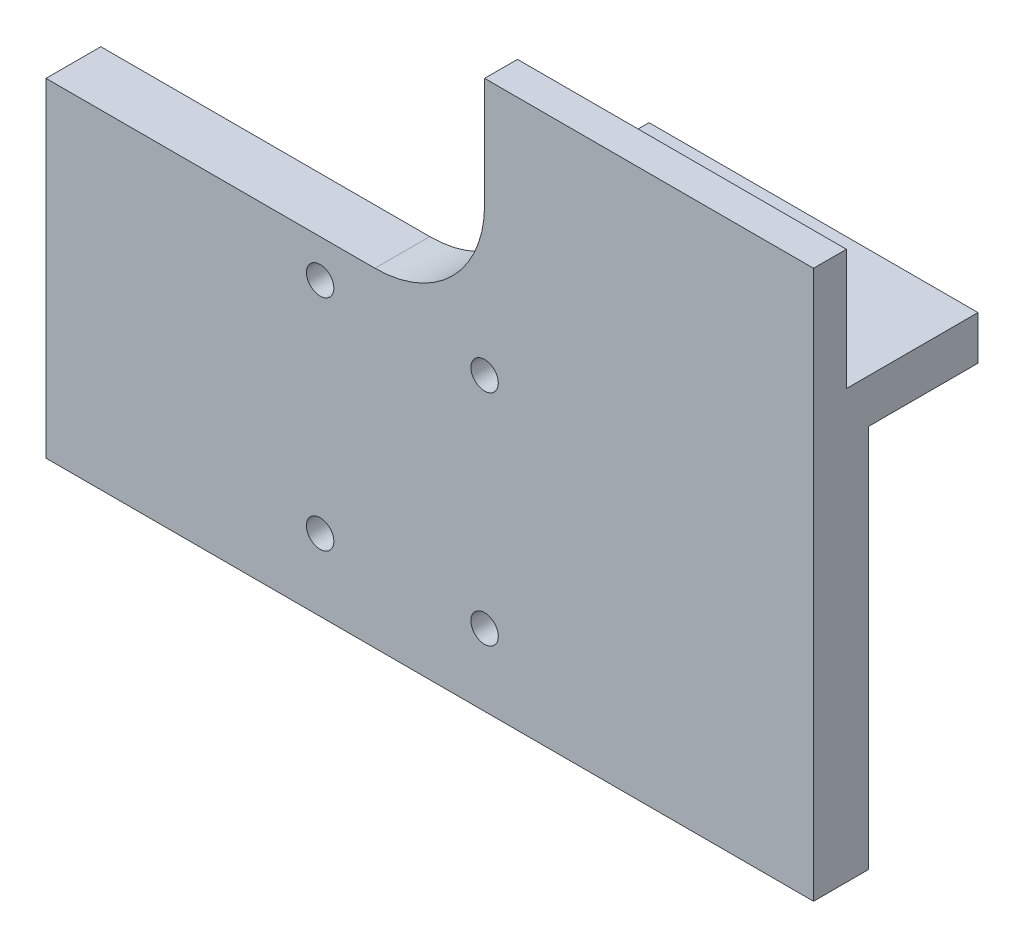
SolidWorks part; units mm, degrees
ref_plane "Front Plane" through (0, 0, 0) normal (0, 0, 1) x (1, 0, 0)
ref_plane "Top Plane" through (0, 0, 0) normal (0, 1, 0) x (1, 0, 0)
ref_plane "Right Plane" through (0, 0, 0) normal (1, 0, 0) x (0, 0, -1)
sketch "Sketch1" plane through (0, 0, 0) normal (0, 0, 1) x (1, 0, 0)
  line L0 (0, 0) -> (70, 0)
  line L1 (0, 0) -> (0, 30)
  line L2 (0, 30) -> (30, 30)
  line L4 (70, 50) -> (70, 0)
  line L5 (40, 40) -> (40, 50)
  line L6 (40, 50) -> (70, 50)
  arc A0 (30, 30) -> (40, 40) centre (30, 40) ccw
  dimension "D2" = 10
  dimension "D3" = 50
  dimension "D1" = 70
  dimension "D5" = 30
  dimension "D6" = 30
extrude "Body" add sketch "Sketch1" along normal blind 5
hole_wizard "M3x0.5 Tapped Hole1" positions "Sketch7" profile "Sketch8" tap size "M3x0.5" standard "ANSI Metric" end condition through all
sketch "Sketch7" plane through (0, 0, 5) normal (0, 0, 1) x (1, 0, 0)
  line L0 (0, 30) -> (0, 0) construction
  line L1 (0, 0) -> (70, 0) construction
  point P0 (25, 6.55)
  dimension "D1" = 25
  dimension "D2" = 6.55
cosmetic thread "Hole Thread5" parameters "D2"=3
sketch "Sketch8" plane through (25, 6.55, 5) normal (1, 0, 0) x (0, -1, 0)
  line L0 (0, 0) -> (0, 5)
  line L1 (0, 5) -> (1.525, 5)
  line L2 (1.25, 4.725) -> (1.25, 0)
  line L5 (1.25, 0) -> (0, 0)
  line L7 (1.525, 5) -> (1.25, 4.725)
  line L8 (-1.525, 5) -> (-1.25, 4.725) construction
  line L11 (0, -6.35) -> (0, 107.95) construction
  dimension "Thru Tap Drill Dia." = 2.5
  dimension "Thru Tap Drill Depth" = 5
  dimension "Far C'Sink Dia." = 3.05
  dimension "Far C'Sink Angle" = 90
pattern_linear "LPattern1" count 2 spacing 15 along (1, 0, 0) count 2 spacing 20 along (0, 1, 0) of "M3x0.5 Tapped Hole1"
cosmetic thread "Hole Thread6" parameters "D2"=3
cosmetic thread "Hole Thread7" parameters "D2"=3
cosmetic thread "Hole Thread8" parameters "D2"=3
sketch "Sketch4" plane through (0, 50, 0) normal (0, 1, 0) x (1, 0, 0)
  line L0 (70, -5) -> (70, 0) construction
  line L1 (40, 0) -> (70, 0)
  line L2 (40, 0) -> (40, -2)
  line L3 (40, -2) -> (70, -2)
  line L4 (70, 0) -> (70, -2)
  dimension "D1" = 2
extrude "Cut-Extrude2" cut sketch "Sketch4" against normal blind 12
sketch "Sketch5" plane through (0, 0, 2) normal (0, 0, -1) x (-1, 0, 0)
  line L0 (-40, 40) -> (-40, 50) construction
  line L1 (-70, 38) -> (-40, 38)
  line L2 (-70, 38) -> (-70, 39)
  line L3 (-70, 39) -> (-40, 39)
  line L4 (-40, 38) -> (-40, 39)
  dimension "D1" = 1
extrude "Boss-Extrude3" add sketch "Sketch5" along normal blind 12
sketch "Sketch6" plane through (0, 38, 0) normal (0, -1, 0) x (1, 0, 0)
  line L4 (70, -10) -> (70, 0)
  line L5 (70, 0) -> (40, 0)
  line L6 (40, 0) -> (40, -10)
  line L7 (40, -10) -> (70, -10)
  line L8 (70, -10) -> (70, 0)
  line L9 (70, 0) -> (40, 0)
  line L10 (40, 0) -> (40, -10)
  line L11 (40, -10) -> (70, -10)
  dimension "D1" = 0
extrude "Boss-Extrude4" add sketch "Sketch6" along normal blind 3
